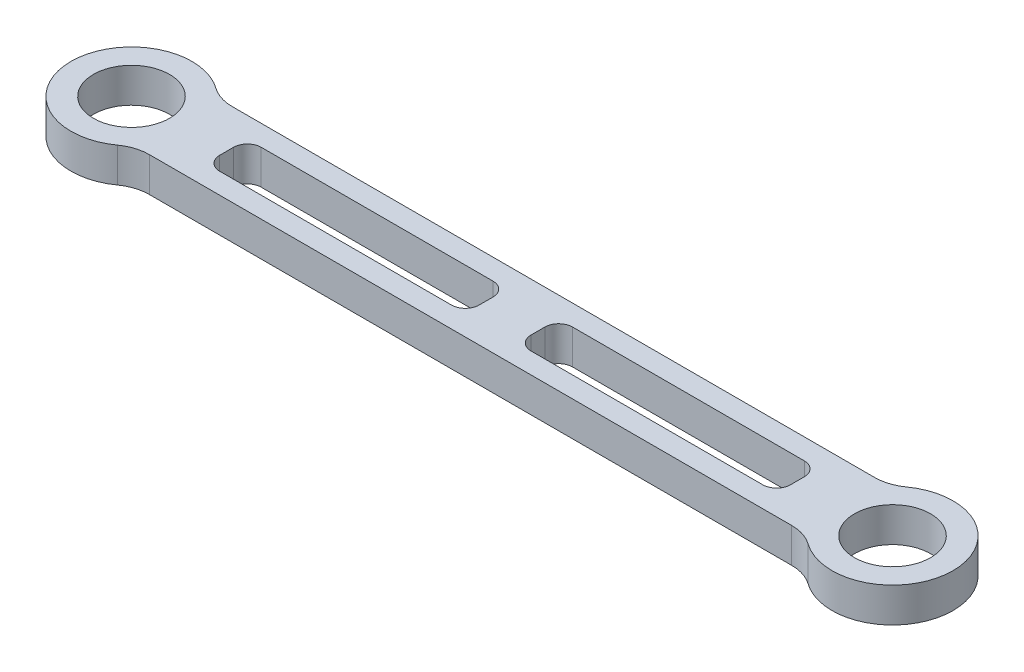
SolidWorks part; units mm, degrees
ref_plane "Front Plane" through (0, 0, 0) normal (0, 0, 1) x (1, 0, 0)
ref_plane "Top Plane" through (0, 0, 0) normal (0, 1, 0) x (1, 0, 0)
ref_plane "Right Plane" through (0, 0, 0) normal (1, 0, 0) x (0, 0, -1)
sketch "Sketch1" plane through (0, 0, 0) normal (0, 1, 0) x (1, 0, 0)
  line L0 (-36.9974, 0) -> (35.0826, 0) construction
  line L1 (12.7377, 12) -> (207.2623, 12)
  line L2 (12.7377, -12) -> (207.2623, -12)
  line L3 (110, 12) -> (110, -12) construction
  line L4 (27.5, 6) -> (102.5, 6)
  line L5 (27.5, 6) -> (27.5, -6)
  line L6 (27.5, -6) -> (102.5, -6)
  line L7 (102.5, 6) -> (102.5, -6)
  line L8 (27.5, 6) -> (102.5, -6) construction
  line L9 (27.5, -6) -> (102.5, 6) construction
  line L10 (192.5, -6) -> (117.5, 6) construction
  line L11 (192.5, 6) -> (117.5, -6) construction
  line L12 (117.5, 6) -> (117.5, -6)
  line L13 (192.5, -6) -> (117.5, -6)
  line L14 (192.5, 6) -> (192.5, -6)
  line L15 (192.5, 6) -> (117.5, 6)
  line L16 (220, 0) -> (256.3474, 70.3916) construction
  line L17 (249.5347, 35.4022) -> (233.5347, 26.2118)
  line L18 (245.3796, 60.0489) -> (254.265, 55.4609)
  line L19 (256.4137, 48.7242) -> (235.4745, 8.1726)
  line L20 (211.9804, 36.7789) -> (207.3924, 27.8935)
  line L21 (207.3924, 27.8935) -> (214.5007, 24.2231)
  line L22 (214.5007, 24.2231) -> (219.0887, 33.1085)
  line L23 (219.0887, 33.1085) -> (211.9804, 36.7789)
  line L24 (207.3924, 27.8935) -> (219.0887, 33.1085) construction
  line L25 (211.9804, 36.7789) -> (214.5007, 24.2231) construction
  line L26 (213.2406, 30.501) -> (236.0165, 18.7404) construction
  line L27 (204.8721, 40.4493) -> (197.0725, 25.3442)
  line L28 (197.0725, 25.3442) -> (197.0725, 12)
  line L29 (215.6509, 43.8872) -> (217.428, 42.9696)
  line L30 (233.5961, 48.1264) -> (238.6429, 57.9003)
  line L31 (233.5347, 26.2118) -> (228.0291, 15.5494)
  circle A0 centre (0, 0) radius 17.5
  circle A1 centre (220, 0) radius 17.5
  circle A2 centre (220, 0) radius 11
  circle A3 centre (0, 0) radius 11
  circle A4 centre (244.7755, 47.981) radius 2.5
  arc A5 (215.6509, 43.8872) -> (204.8721, 40.4493) centre (211.9804, 36.7789) ccw
  arc A6 (233.5961, 48.1264) -> (217.428, 42.9696) centre (222.9336, 53.632) cw
  arc A7 (256.4137, 48.7242) -> (254.265, 55.4609) centre (251.971, 51.0182) ccw
  arc A8 (238.6429, 57.9003) -> (245.3796, 60.0489) centre (243.0856, 55.6063) cw
  point P13 (65, 0)
  point P24 (155, 0)
  point P44 (208.5426, 47.5576)
  dimension "D2" = 22
  dimension "D3" = 35
  dimension "D12" = 5
  dimension "D20" = 8
  dimension "D22" = 12
  dimension "D23" = 5
  dimension "D1" = 220
  dimension "D4" = 12
  dimension "D5" = 12
  dimension "D6" = 75
  dimension "D7" = 45
  dimension "D8" = 117.31
  dimension "D9" = 10
  dimension "D10" = 54
  dimension "D11" = 65
  dimension "D13" = 10
  dimension "D14" = 8
  dimension "D15" = 30
  dimension "D16" = 16
  dimension "D17" = 8
  dimension "D18" = 8
  dimension "D19" = 25
  dimension "D21" = 10
  dimension "D24" = 12
  dimension "D25" = 16
extrude "Boss-Extrude1" add sketch "Sketch1" along normal blind 10 contours A1 L1 A0 L2 L4 L7 L6 L5 L15 L14 L13 L12 | A0 A3 | A1 A2
fillet "Fillet1" radius 4 8 edges at (102.5, 5, -6) (192.5, 5, 6) (192.5, 5, -6) (117.5, 5, 6) (117.5, 5, -6) (27.5, 5, 6) (27.5, 5, -6) (102.5, 5, 6)
fillet "Fillet2" radius 12 4 edges at (207.2623, 5, 12) (207.2623, 5, -12) (12.7377, 5, -12) (12.7377, 5, 12)
